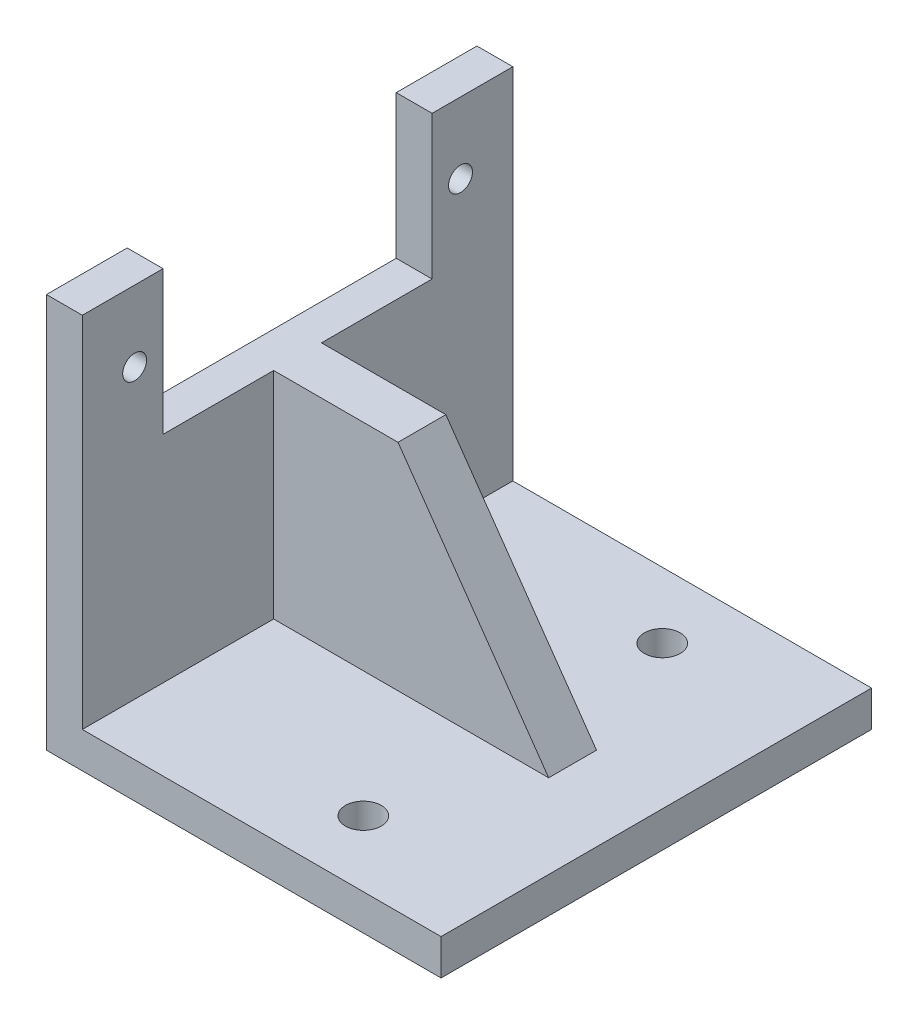
SolidWorks part; units mm, degrees
ref_plane "Front Plane" through (0, 0, 0) normal (0, 0, 1) x (1, 0, 0)
ref_plane "Top Plane" through (0, 0, 0) normal (0, 1, 0) x (1, 0, 0)
ref_plane "Right Plane" through (0, 0, 0) normal (1, 0, 0) x (0, 0, -1)
sketch "Sketch1" plane through (0, 0, 0) normal (0, 0, 1) x (1, 0, 0)
  line L0 (0, 0) -> (0, 30)
  line L1 (0, 0) -> (30, 0)
  dimension "D1" = 30
  dimension "D2" = 30
extrude "Extrude-Thin1" add sketch "Sketch1" along normal mid plane 36 thin thin type one direction wall 3
sketch "Sketch2" plane through (0, 0, 0) normal (1, 0, 0) x (0, 0, -1)
  line L0 (0, 0) -> (0, 48) construction
  line L1 (-18, 30) -> (18, 30) construction
  line L2 (-11.25, 18) -> (11.25, 18)
  line L3 (-11.25, 18) -> (-11.25, 30)
  line L4 (-11.25, 30) -> (11.25, 30)
  line L5 (11.25, 18) -> (11.25, 30)
  line L6 (-11.25, 18) -> (11.25, 30) construction
  line L7 (-11.25, 30) -> (11.25, 18) construction
  point P2 (0, 24)
  point P10 (0, 30)
  dimension "D1" = 22.5
  dimension "D2" = 12
extrude "Cut-Extrude1" cut sketch "Sketch2" against normal through all
sketch "Sketch3" plane through (0, 0, 0) normal (1, 0, 0) x (0, 0, -1)
  line L0 (0, 0) -> (0, 44.5323) construction
  circle A0 centre (13.625, 24.0694) radius 1
  circle A1 centre (-13.625, 24.0694) radius 1
  dimension "D1" = 2
  dimension "D2" = 27.25
extrude "Cut-Extrude2" cut sketch "Sketch3" against normal through all
sketch "Sketch6" plane through (0, 0, 0) normal (0, 1, 0) x (1, 0, 0)
  line L0 (0, 0) -> (38.6321, 0) construction
  line L1 (0, -18) -> (0, 18) construction
  line L2 (23, -2) -> (0, -2)
  line L3 (23, -2) -> (23, 2)
  line L4 (23, 2) -> (0, 2)
  line L5 (0, -2) -> (0, 2)
  line L6 (23, -2) -> (0, 2) construction
  line L7 (23, 2) -> (0, -2) construction
  point P3 (11.5, 0)
  dimension "D1" = 23
  dimension "D2" = 4
extrude "Boss-Extrude1" add sketch "Sketch6" along normal blind 18
sketch "Sketch7" plane through (0, 0, -2) normal (0, 0, -1) x (-1, 0, 0)
  line L0 (-10.3996, 18) -> (-23, 18)
  line L1 (-23, 18) -> (0, 18) construction
  line L2 (-23, 18) -> (-23, 0)
  line L3 (-23, 0) -> (-10.3996, 18)
  point P5 (0, 0)
  point P9 (0, 0)
  point P10 (-10.1, 18)
extrude "Cut-Extrude3" cut sketch "Sketch7" against normal through all
sketch "Sketch8" plane through (0, 0, 0) normal (0, 1, 0) x (1, 0, 0)
  line L0 (0, 0) -> (40.1568, 0) construction
  line L1 (30, -18) -> (30, 18) construction
  circle A0 centre (18, 12.5) radius 1.5
  circle A1 centre (18, -12.5) radius 1.5
  dimension "D1" = 3
  dimension "D2" = 25
  dimension "D3" = 12
extrude "Cut-Extrude4" cut sketch "Sketch8" against normal through all
